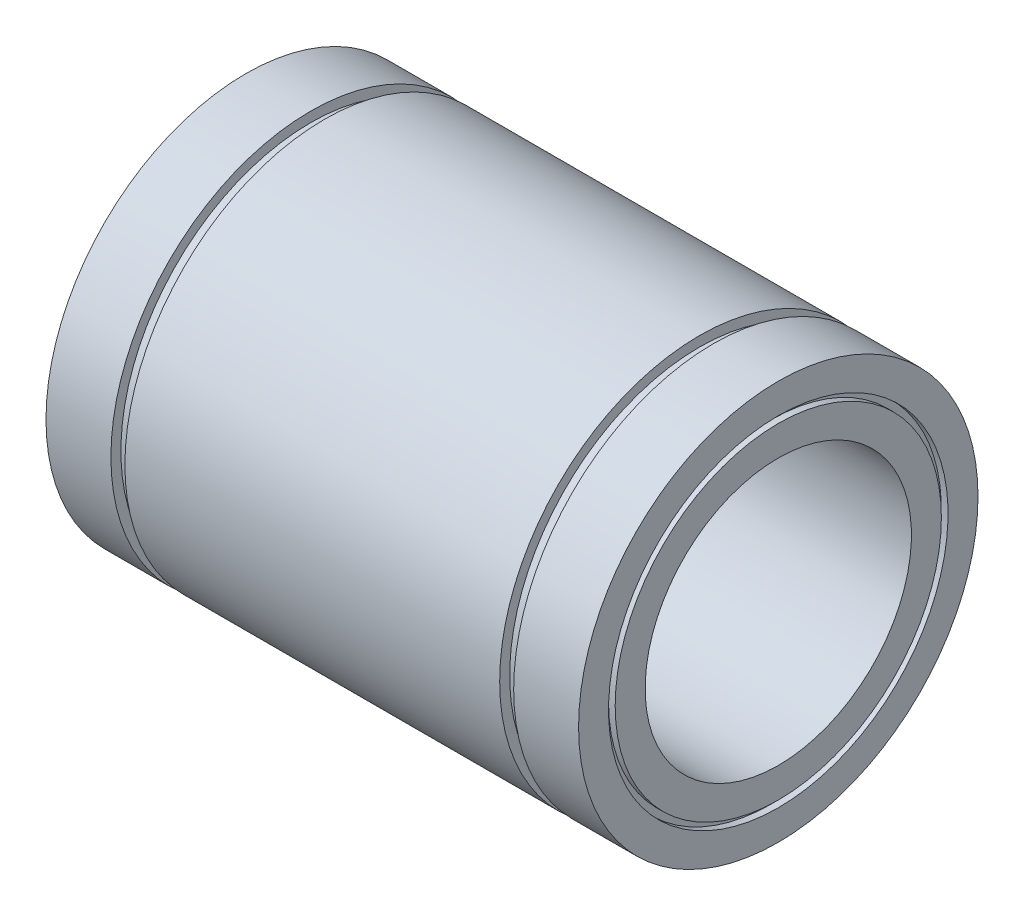
SolidWorks part; units mm, degrees
material "Ст3сп ГОСТ 535-2005"
ref_plane "Plano frontal" through (0, 0, 0) normal (0, 0, 1) x (1, 0, 0)
ref_plane "Plano superior" through (0, 0, 0) normal (0, 1, 0) x (1, 0, 0)
ref_plane "Plano direito" through (0, 0, 0) normal (1, 0, 0) x (0, 0, -1)
sketch "Esboço1" plane through (0, 0, 0) normal (0, 0, 1) x (1, 0, 0)
  line L0 (-40, 30) -> (-30.25, 30)
  line L1 (-30.25, 30) -> (-30.25, 28.5)
  line L2 (-30.25, 28.5) -> (-28.15, 28.5)
  line L3 (-28.15, 28.5) -> (-28.15, 30)
  line L4 (-28.15, 30) -> (28.15, 30)
  line L5 (28.15, 30) -> (28.15, 28.5)
  line L6 (28.15, 28.5) -> (30.25, 28.5)
  line L7 (30.25, 28.5) -> (30.25, 30)
  line L8 (30.25, 30) -> (40, 30)
  line L9 (40, 30) -> (40, 25.5)
  line L10 (40, 20) -> (-40, 20)
  line L11 (-40, 20) -> (-40, 24.5)
  line L12 (0, 20) -> (0, 0) construction
  line L13 (0, 0) -> (-86.5, 0) construction
  line L14 (-40, 25.5) -> (-40, 30)
  line L15 (-40, 25.5) -> (-39, 25.5)
  line L16 (40, 24.5) -> (40, 20)
  line L17 (-39, 25.5) -> (-39, 24.5)
  line L18 (-39, 24.5) -> (-40, 24.5)
  line L19 (40, 25.5) -> (39, 25.5)
  line L21 (40, 24.5) -> (39, 24.5)
  line L22 (39, 25.5) -> (39, 24.5)
  dimension "D1" = 80
  dimension "D2" = 60.5
  dimension "D3" = 2.1
  dimension "D4" = 40
  dimension "D5" = 60
  dimension "D6" = 57
  dimension "D7" = 1
  dimension "D8" = 1
  dimension "D9" = 1
  dimension "D10" = 1
revolve "Revolução1" add sketch "Esboço1" angle 360 about L13
